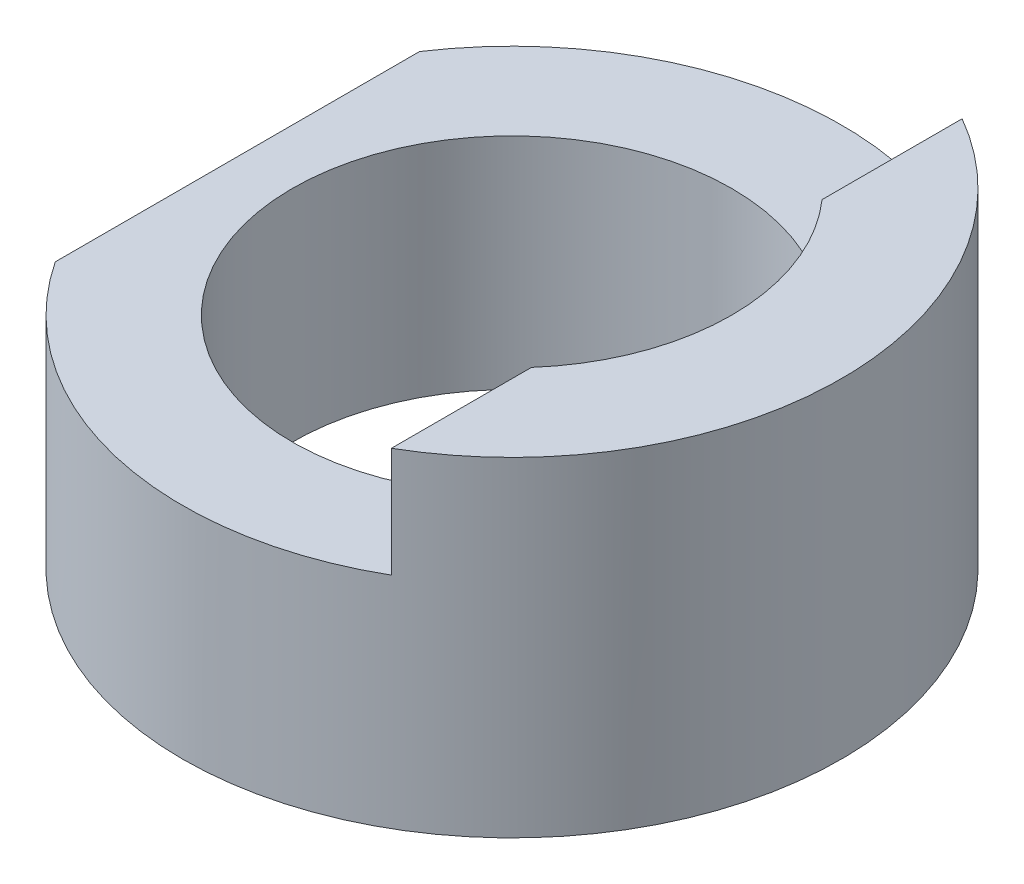
SolidWorks part; units mm, degrees
ref_plane "Front Plane" through (0, 0, 0) normal (0, 0, 1) x (1, 0, 0)
ref_plane "Top Plane" through (0, 0, 0) normal (0, 1, 0) x (1, 0, 0)
ref_plane "Right Plane" through (0, 0, 0) normal (1, 0, 0) x (0, 0, -1)
sketch "Sketch1" plane through (0, 0, 0) normal (0, 0, 1) x (1, 0, 0)
  line L1 (0, 0) -> (120, 0)
  line L2 (0, 0) -> (0, 60)
  line L3 (0, 60) -> (120, 60)
  line L4 (120, 0) -> (120, 60)
  dimension "D1" = 120
  dimension "D2" = 60
extrude "Boss-Extrude1" add sketch "Sketch1" along normal blind 120
sketch "Sketch2" plane through (0, 0, 120) normal (0, 0, 1) x (1, 0, 0)
  line L0 (0, 14.8178) -> (0, 20)
  line L1 (0, 60) -> (0, 0) construction
  line L2 (0, 20) -> (10, 20)
  line L3 (10, 20) -> (10, 40)
  line L4 (10, 40) -> (90, 40)
  line L5 (90, 40) -> (90, 60)
  line L6 (120, 60) -> (0, 60) construction
  line L7 (90, 60) -> (120, 60)
  line L8 (90, 60) -> (0, 60)
  line L9 (0, 60) -> (0, 20)
  line M1 (0, 60) -> (0, 0)
  line M4 (120, 60) -> (0, 60)
  dimension "D1" = 10
  dimension "D2" = 20
  dimension "D3" = 20
  dimension "D4" = 30
extrude "Cut-Extrude1" cut sketch "Sketch2" against normal blind 120 contours L4 L5 L2 L3 M4 M1
sketch "Sketch3" plane through (0, 0, 0) normal (0, 1, 0) x (1, 0, 0)
  line L0 (120, -120) -> (120, 0) construction
  line L1 (0, 0) -> (120, 0) construction
  line L2 (60, 0) -> (120, 0)
  line L3 (120, 0) -> (120, -120)
  line L4 (120, -120) -> (0, -120)
  line L5 (0, -120) -> (0, 0)
  line L6 (0, 0) -> (60, 0)
  circle A0 centre (60, -60) radius 60
  dimension "D1" = 120
  dimension "D2" = 60
  dimension "D3" = 60
  dimension "D4" = 60
  dimension "D5" = 60
  dimension "D6" = 120
  dimension "D7" = 120
  dimension "D8" = 120
  dimension "D9" = 60
  dimension "D10" = 60
extrude "Cut-Extrude2" cut sketch "Sketch3" along normal blind 120 contours A0 L3 L2 | A0 L6 L5 | A0 L5 L4 | A0 L4 L3
sketch "Sketch5" plane through (0, 0, 0) normal (0, -1, 0) x (-1, 0, 0)
  circle A0 centre (-60, -60) radius 40
  circle A1 centre (-60, -60) radius 60 construction
  dimension "D1" = 80
  dimension "D2" = 0
extrude "Cut-Extrude3" cut sketch "Sketch5" against normal blind 120
